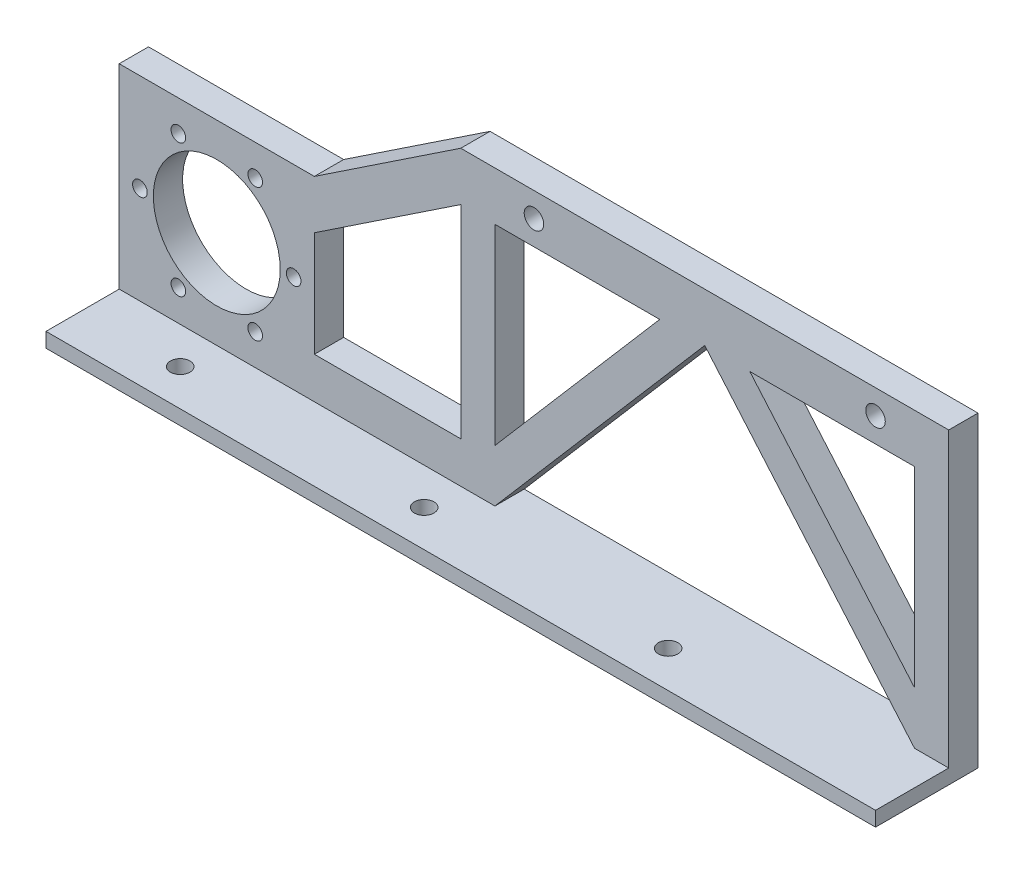
SolidWorks part; units mm, degrees
ref_plane "Front Plane" through (0, 0, 0) normal (0, 0, 1) x (1, 0, 0)
ref_plane "Top Plane" through (0, 0, 0) normal (0, 1, 0) x (1, 0, 0)
ref_plane "Right Plane" through (0, 0, 0) normal (1, 0, 0) x (0, 0, -1)
sketch "Sketch1" plane through (0, 0, 0) normal (0, 0, 1) x (1, 0, 0)
  line L0 (-35, 0) -> (35, 0)
  line L1 (-50, 5) -> (50, 5)
  line L2 (-50, 5) -> (-50, -5)
  line L3 (-50, -5) -> (50, -5)
  line L4 (50, 5) -> (50, -5)
  line L5 (-50, 5) -> (50, -5) construction
  line L6 (-50, -5) -> (50, 5) construction
  line L7 (-50, -5) -> (-43, -5)
  line L8 (-50, -5) -> (-50, -55)
  line L9 (-50, -55) -> (-43, -55)
  line L10 (-43, -5) -> (-43, -55)
  line L11 (50, -5) -> (43, -5)
  line L12 (50, -5) -> (50, -55)
  line L13 (50, -55) -> (43, -55)
  line L14 (43, -5) -> (43, -55)
  line L15 (-43, -55) -> (0, -5)
  line L16 (0, -5) -> (43, -55)
  line L17 (-43, -44.2645) -> (-9.2326, -5)
  line L18 (9.2326, -5) -> (43, -44.2645)
  line L19 (-120, -55) -> (-80, -15) construction
  line L20 (-50, -55) -> (-80, -55)
  line L21 (-50, -55) -> (-50, -46.5716)
  line L22 (-50, -46.5716) -> (-80, -46.5716)
  line L23 (-80, -55) -> (-80, -46.5716)
  line L24 (-80, -55) -> (-120, -55)
  line L25 (-80, -55) -> (-80, -15)
  line L26 (-80, -15) -> (-120, -15)
  line L27 (-120, -55) -> (-120, -15)
  line L28 (-80, -15) -> (-50, 5)
  line L29 (-50, -5) -> (-80, -25)
  circle A0 centre (35, 0) radius 2
  circle A1 centre (-35, 0) radius 2
  circle A2 centre (-100, -35) radius 13
  circle A3 centre (-100, -35) radius 15.75 construction
  circle A4 centre (-84.25, -35) radius 1.5
  circle A10 centre (-92.125, -48.6399) radius 1.5
  circle A11 centre (-107.875, -48.6399) radius 1.5
  circle A12 centre (-115.75, -35) radius 1.5
  circle A13 centre (-107.875, -21.3601) radius 1.5
  circle A14 centre (-92.125, -21.3601) radius 1.5
  point P0 (0, 0)
  point P15 (0, 0)
  point P17 (-50, 0)
  point P46 (-134.6167, -35)
  point P49 (-100, -35)
  dimension "D2" = 4
  dimension "D3" = 4
  dimension "D13" = 6
  dimension "D1" = 70
  dimension "D4" = 15
  dimension "D5" = 10
  dimension "D6" = 7
  dimension "D7" = 7
  dimension "D8" = 7
  dimension "D9" = 7
  dimension "D10" = 50
  dimension "D11" = 40
  dimension "D12" = 40
  dimension "D14" = 30
extrude "Boss-Extrude1" add sketch "Sketch1" along normal blind 6
sketch "Sketch2" plane through (0, 0, 6) normal (0, 0, 1) x (1, 0, 0)
  line L1 (-120, -55) -> (50, -55)
  line L2 (-120, -55) -> (-120, -58)
  line L3 (-120, -58) -> (50, -58)
  line L4 (50, -55) -> (50, -58)
  dimension "D1" = 3
extrude "Boss-Extrude2" add sketch "Sketch2" along normal blind 15 and the other way up to vertex (6 mm away) other way up to point (-120, -55, 0)
sketch "Sketch3" plane through (0, -55, 0) normal (0, 1, 0) x (1, 0, 0)
  line L0 (-120, -13.5) -> (50, -13.5) construction
  line L1 (-120, -6) -> (-120, -21) construction
  line L2 (50, -6) -> (50, -21) construction
  line L3 (-170, -13.5) -> (0, -13.5) construction
  line L4 (-220, -13.5) -> (-50, -13.5) construction
  circle A0 centre (0, -13.5) radius 2
  circle A1 centre (-50, -13.5) radius 2
  circle A2 centre (-100, -13.5) radius 2
  dimension "D2" = 4
  dimension "D1" = 50
  dimension "D3" = 3
extrude "Cut-Extrude1" cut sketch "Sketch3" against normal blind 15
